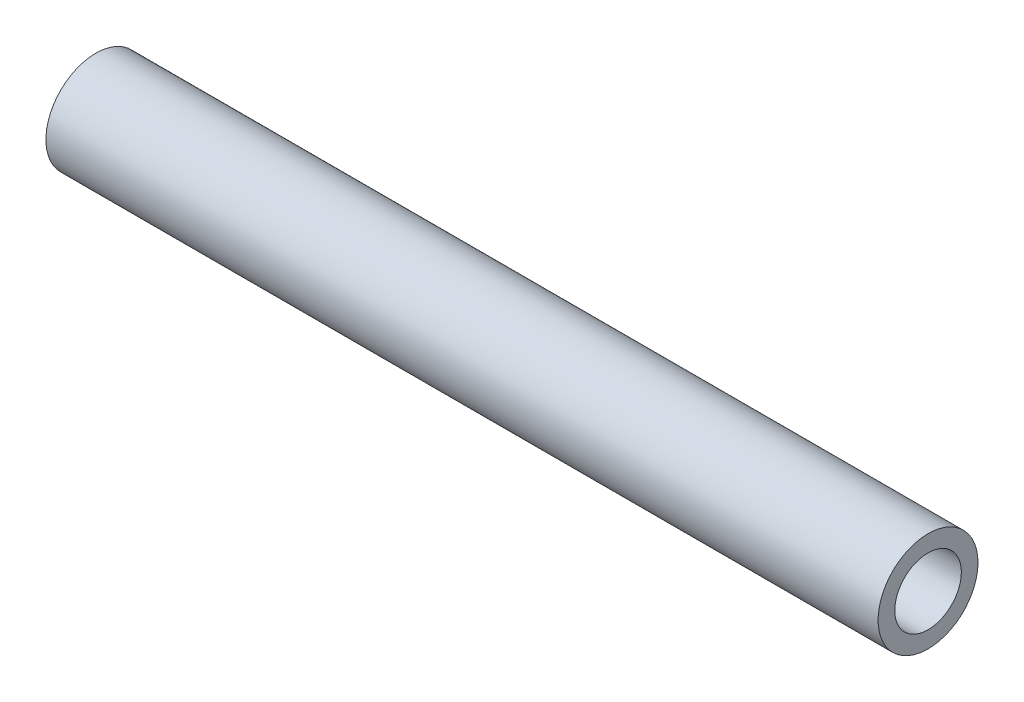
SolidWorks part; units mm, degrees
material "PC Alta Viscosidade"
ref_plane "Front" through (0, 0, 0) normal (0, 0, 1) x (1, 0, 0)
ref_plane "Top" through (0, 0, 0) normal (0, 1, 0) x (1, 0, 0)
ref_plane "Right" through (0, 0, 0) normal (1, 0, 0) x (0, 0, -1)
sketch "Esboço1" plane through (0, 0, 0) normal (1, 0, 0) x (0, 0, -1)
  circle A0 centre (0, 0) radius 6
  circle A1 centre (0, 0) radius 4
extrude "Ressalto-extrusão1" add sketch "Esboço1" along normal mid plane 100
